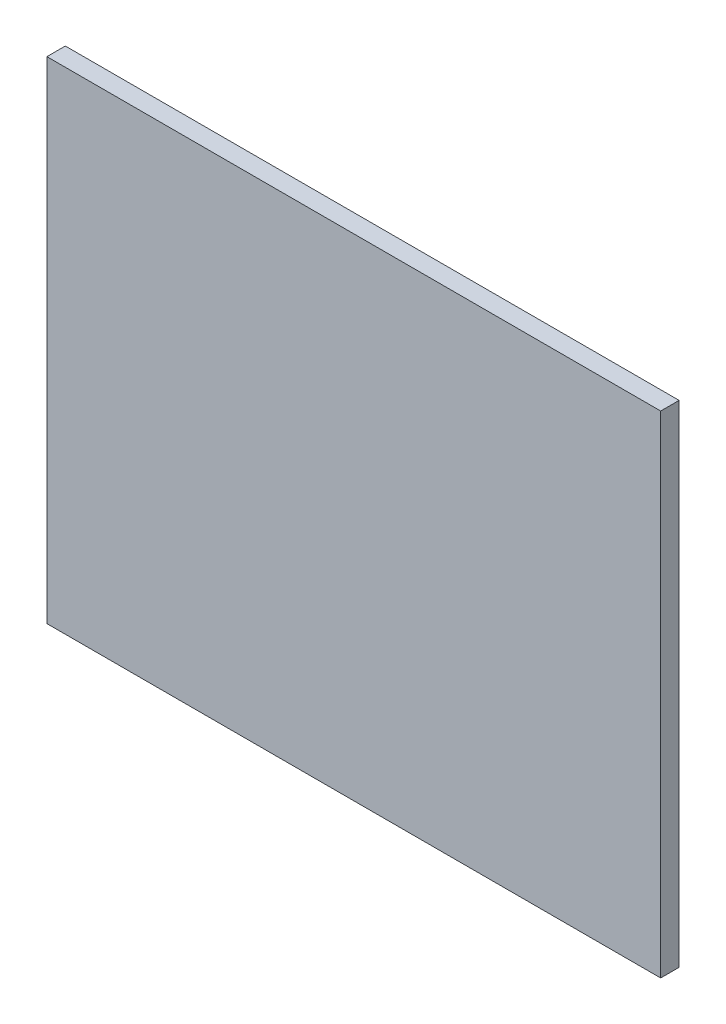
SolidWorks part; units mm, degrees
material "Cobre"
ref_plane "Plano frontal" through (0, 0, 0) normal (0, 0, 1) x (1, 0, 0)
ref_plane "Plano superior" through (0, 0, 0) normal (0, 1, 0) x (1, 0, 0)
ref_plane "Plano direito" through (0, 0, 0) normal (1, 0, 0) x (0, 0, -1)
sketch "Esboço1" plane through (0, 0, 0) normal (0, 0, 1) x (1, 0, 0)
  line L1 (-5.3521, 3.2394) -> (94.6479, 3.2394)
  line L2 (-5.3521, 3.2394) -> (-5.3521, -76.7606)
  line L3 (-5.3521, -76.7606) -> (94.6479, -76.7606)
  line L4 (94.6479, 3.2394) -> (94.6479, -76.7606)
  dimension "D1" = 80
  dimension "D2" = 100
extrude "Ressalto-extrusão1" add sketch "Esboço1" along normal blind 3
